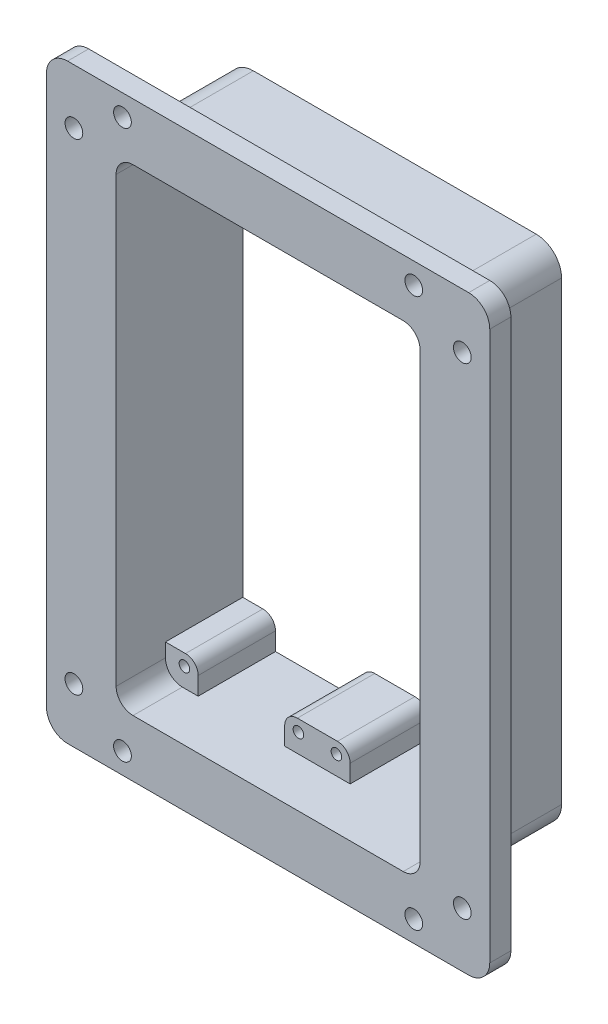
SolidWorks part; units mm, degrees
other "Markup1"
sketch "Sketch3" plane through (50, 70, 5) normal (0.4181, 0.0765, 0.9052) x (0.9081, -0.012, -0.4185)
ref_plane "Front Plane" through (0, 0, 0) normal (0, 0, 1) x (1, 0, 0)
ref_plane "Top Plane" through (0, 0, 0) normal (0, 1, 0) x (1, 0, 0)
ref_plane "Right Plane" through (0, 0, 0) normal (1, 0, 0) x (0, 0, -1)
sketch "Sketch1" plane through (0, 0, 0) normal (0, 0, 1) x (1, 0, 0)
  line L1 (-47.5, 70) -> (47.5, 70)
  line L2 (-52.5, 65) -> (-52.5, -65)
  line L3 (-47.5, -70) -> (47.5, -70)
  line L4 (52.5, 65) -> (52.5, -65)
  line L5 (-52.5, 70) -> (52.5, -70) construction
  line L6 (-52.5, -70) -> (52.5, 70) construction
  line L7 (-32, 56.5) -> (32, 56.5)
  line L8 (-36, 52.5) -> (-36, -52.5)
  line L9 (-32, -56.5) -> (32, -56.5)
  line L10 (36, 52.5) -> (36, -52.5)
  line L11 (-36, 56.5) -> (36, -56.5) construction
  line L12 (-36, -56.5) -> (36, 56.5) construction
  arc A0 (-36, -52.5) -> (-32, -56.5) centre (-32, -52.5) ccw
  arc A1 (32, -56.5) -> (36, -52.5) centre (32, -52.5) ccw
  arc A2 (32, 56.5) -> (36, 52.5) centre (32, 52.5) cw
  arc A3 (-32, 56.5) -> (-36, 52.5) centre (-32, 52.5) ccw
  arc A4 (-52.5, -65) -> (-47.5, -70) centre (-47.5, -65) ccw
  arc A5 (47.5, -70) -> (52.5, -65) centre (47.5, -65) ccw
  arc A6 (47.5, 70) -> (52.5, 65) centre (47.5, 65) cw
  arc A7 (-47.5, 70) -> (-52.5, 65) centre (-47.5, 65) ccw
  point P0 (0, 0)
  point P6 (0, 0)
  dimension "D5" = 4
  dimension "D6" = 5
  dimension "D1" = 105
  dimension "D2" = 140
  dimension "D3" = 113
  dimension "D4" = 72
extrude "Boss-Extrude1" add sketch "Sketch1" along normal blind 5
sketch "Sketch2" plane through (0, 0, 0) normal (0, 0, -1) x (-1, 0, 0)
  line L1 (-33.5, 60) -> (33.5, 60)
  line L2 (-39.5, 54) -> (-39.5, -54)
  line L3 (-33.5, -60) -> (33.5, -60)
  line L4 (39.5, 54) -> (39.5, -54)
  line L5 (-39.5, 60) -> (39.5, -60) construction
  line L6 (-39.5, -60) -> (39.5, 60) construction
  arc A0 (-39.5, -54) -> (-33.5, -60) centre (-33.5, -54) ccw
  arc A1 (33.5, -60) -> (39.5, -54) centre (33.5, -54) ccw
  arc A2 (33.5, 60) -> (39.5, 54) centre (33.5, 54) cw
  arc A3 (-33.5, 60) -> (-39.5, 54) centre (-33.5, 54) ccw
  point P0 (0, 0)
  dimension "D3" = 6
  dimension "D1" = 79
  dimension "D2" = 120
extrude "Boss-Extrude2" add sketch "Sketch2" along normal blind 25
sketch "Sketch4" plane through (0, 0, 5) normal (0, 0, 1) x (1, 0, 0)
  line L0 (47.5, 70) -> (-47.5, 70) construction
  line L1 (52.5, -65) -> (52.5, 65) construction
  line L2 (0, 70) -> (0, -70) construction
  line L3 (-47.5, -70) -> (47.5, -70) construction
  line L4 (0, 0) -> (52.5, 0) construction
  circle A0 centre (34.5, 65) radius 2.1
  circle A1 centre (-34.5, 65) radius 2.1
  circle A2 centre (-34.5, -65) radius 2.1
  circle A3 centre (34.5, -65) radius 2.1
  dimension "D3" = 4.2
  dimension "D1" = 5
  dimension "D2" = 18
extrude "Cut-Extrude1" cut sketch "Sketch4" against normal up to next
sketch "Sketch5" plane through (0, 0, 0) normal (0, 0, 1) x (1, 0, 0)
  line L1 (-32, 56.5) -> (32, 56.5)
  line L2 (-36, 52.5) -> (-36, -52.5)
  line L3 (-32, -56.5) -> (32, -56.5)
  line L4 (36, 52.5) -> (36, -52.5)
  line L5 (-36, 56.5) -> (36, -56.5) construction
  line L6 (-36, -56.5) -> (36, 56.5) construction
  arc A0 (32, -56.5) -> (36, -52.5) centre (32, -52.5) ccw
  arc A1 (-36, -52.5) -> (-32, -56.5) centre (-32, -52.5) ccw
  arc A2 (32, 56.5) -> (36, 52.5) centre (32, 52.5) cw
  arc A3 (-32, 56.5) -> (-36, 52.5) centre (-32, 52.5) ccw
  point P0 (0, 0)
  dimension "D3" = 4
  dimension "D1" = 72
  dimension "D2" = 113
extrude "Cut-Extrude2" cut sketch "Sketch5" against normal up to next
sketch "Sketch8" plane through (0, 0, -25) normal (0, 0, -1) x (-1, 0, 0)
  line L0 (0, 56.5) -> (0, -56.5) construction
  line L1 (-32, 56.5) -> (32, 56.5) construction
  line L2 (32, -56.5) -> (-32, -56.5) construction
  line L3 (-36, 0) -> (0, 0) construction
  line L4 (-36, -52.5) -> (-36, 52.5) construction
  line L5 (28.25, 52.25) -> (28.25, 56.5)
  line L6 (7.75, 56.5) -> (-7.75, 56.5)
  line L7 (0, 56.5) -> (0, 49.25)
  line L8 (4.75, 49.25) -> (-4.75, 49.25)
  line L9 (-7.75, 56.5) -> (-7.75, 52.25)
  line L10 (-36, 49.25) -> (-31.25, 49.25)
  line L11 (-36, 49.25) -> (-36, 52.5)
  line L12 (-32, 56.5) -> (-28.25, 56.5)
  line L13 (-28.25, 52.25) -> (-28.25, 56.5)
  line L14 (32, 56.5) -> (28.25, 56.5)
  line L15 (36, 49.25) -> (36, 52.5)
  line L16 (36, 49.25) -> (31.25, 49.25)
  line L17 (7.75, 56.5) -> (7.75, 52.25)
  line L18 (7.75, -56.5) -> (7.75, -52.25)
  line L19 (36, -49.25) -> (31.25, -49.25)
  line L20 (36, -49.25) -> (36, -52.5)
  line L21 (32, -56.5) -> (28.25, -56.5)
  line L22 (-28.25, -52.25) -> (-28.25, -56.5)
  line L23 (-32, -56.5) -> (-28.25, -56.5)
  line L24 (-36, -49.25) -> (-36, -52.5)
  line L25 (-36, -49.25) -> (-31.25, -49.25)
  line L26 (-7.75, -56.5) -> (-7.75, -52.25)
  line L27 (4.75, -49.25) -> (-4.75, -49.25)
  line L28 (0, -56.5) -> (0, -49.25)
  line L29 (7.75, -56.5) -> (-7.75, -56.5)
  line L30 (28.25, -52.25) -> (28.25, -56.5)
  arc A0 (-36, 52.5) -> (-32, 56.5) centre (-32, 52.5) cw
  arc A1 (-4.75, 49.25) -> (-7.75, 52.25) centre (-4.75, 52.25) cw
  arc A2 (-31.25, 49.25) -> (-28.25, 52.25) centre (-31.25, 52.25) ccw
  arc A3 (31.25, 49.25) -> (28.25, 52.25) centre (31.25, 52.25) cw
  arc A4 (4.75, 49.25) -> (7.75, 52.25) centre (4.75, 52.25) ccw
  arc A5 (36, 52.5) -> (32, 56.5) centre (32, 52.5) ccw
  arc A6 (36, -52.5) -> (32, -56.5) centre (32, -52.5) cw
  arc A7 (4.75, -49.25) -> (7.75, -52.25) centre (4.75, -52.25) cw
  arc A8 (31.25, -49.25) -> (28.25, -52.25) centre (31.25, -52.25) ccw
  arc A9 (-31.25, -49.25) -> (-28.25, -52.25) centre (-31.25, -52.25) cw
  arc A10 (-4.75, -49.25) -> (-7.75, -52.25) centre (-4.75, -52.25) ccw
  arc A11 (-36, -52.5) -> (-32, -56.5) centre (-32, -52.5) ccw
  point P17 (-33.625, 49.25)
  point P22 (-7.75, 49.25)
  point P25 (-28.25, 49.25)
  point P38 (28.25, 49.25)
  point P39 (7.75, 49.25)
  point P65 (7.75, -49.25)
  point P66 (28.25, -49.25)
  point P67 (-28.25, -49.25)
  point P68 (-7.75, -49.25)
  arc M3 (-32, -56.5) -> (-36, -52.5) centre (-32, -52.5) cw
  line M4 (-36, -52.5) -> (-36, 52.5)
  arc M5 (-36, 52.5) -> (-32, 56.5) centre (-32, 52.5) cw
  line M6 (-32, 56.5) -> (32, 56.5)
  arc M7 (32, 56.5) -> (36, 52.5) centre (32, 52.5) cw
  line M8 (36, 52.5) -> (36, -52.5)
  arc M9 (36, -52.5) -> (32, -56.5) centre (32, -52.5) cw
  line M10 (32, -56.5) -> (-32, -56.5)
  dimension "D3" = 4
  dimension "D6" = 3
  dimension "D1" = 7.75
  dimension "D2" = 7.25
  dimension "D4" = 7.75
  dimension "D5" = 7.25
extrude "Boss-Extrude4" add sketch "Sketch8" against normal blind 18.32 contours L10 A2 L13 M6 M5 M4 | A1 L8 L7 L9 M6 | L8 A4 L17 L6 L7 | A3 L16 L5 M8 M7 M6 | A9 L25 L22 M4 M3 M10 | L27 A10 L26 L28 M10 | A7 L27 L28 L18 M10 | L19 A8 L30 M10 M9 M8
sketch "Sketch9" plane through (0, 0, -6.68) normal (0, 0, 1) x (1, 0, 0)
  line L0 (0, 56.5) -> (0, -56.5) construction
  line L1 (32, 56.5) -> (-32, 56.5) construction
  line L2 (-7.75, -56.5) -> (7.75, -56.5) construction
  line L3 (-4.75, 49.25) -> (4.75, 49.25) construction
  line L4 (-7.75, 56.5) -> (-7.75, 52.25) construction
  line L5 (-18, 0) -> (-18, 56.5) construction
  line L7 (0, 0) -> (-36, 0) construction
  line L8 (-36, 52.5) -> (-36, -52.5) construction
  circle A0 centre (-4.5, 52) radius 1.25
  circle A1 centre (-31.5, 52) radius 1.25
  circle A2 centre (31.5, 52) radius 1.25
  circle A3 centre (4.5, 52) radius 1.25
  circle A4 centre (4.5, -52) radius 1.25
  circle A5 centre (31.5, -52) radius 1.25
  circle A6 centre (-31.5, -52) radius 1.25
  circle A7 centre (-4.5, -52) radius 1.25
  dimension "D1" = 2.5
  dimension "D2" = 2.75
  dimension "D3" = 3.25
extrude "Cut-Extrude3" cut sketch "Sketch9" against normal blind 10
sketch "Sketch10" plane through (0, 0, 5) normal (0, 0, 1) x (1, 0, 0)
  line L0 (-52.5, 65) -> (-52.5, -65) construction
  line L1 (47.5, 70) -> (-47.5, 70) construction
  line L2 (0, 70) -> (0, -70) construction
  line L3 (47.5, 70) -> (-47.5, 70) construction
  line L4 (-47.5, -70) -> (47.5, -70) construction
  line L5 (-52.5, 0) -> (52.5, 0) construction
  line L6 (52.5, -65) -> (52.5, 65) construction
  circle A0 centre (-46, 57) radius 2.1
  circle A1 centre (46, 57) radius 2.1
  circle A2 centre (46, -57) radius 2.1
  circle A3 centre (-46, -57) radius 2.1
  dimension "D1" = 4.2
  dimension "D2" = 6.5
  dimension "D3" = 13
extrude "Cut-Extrude4" cut sketch "Sketch10" against normal up to next
